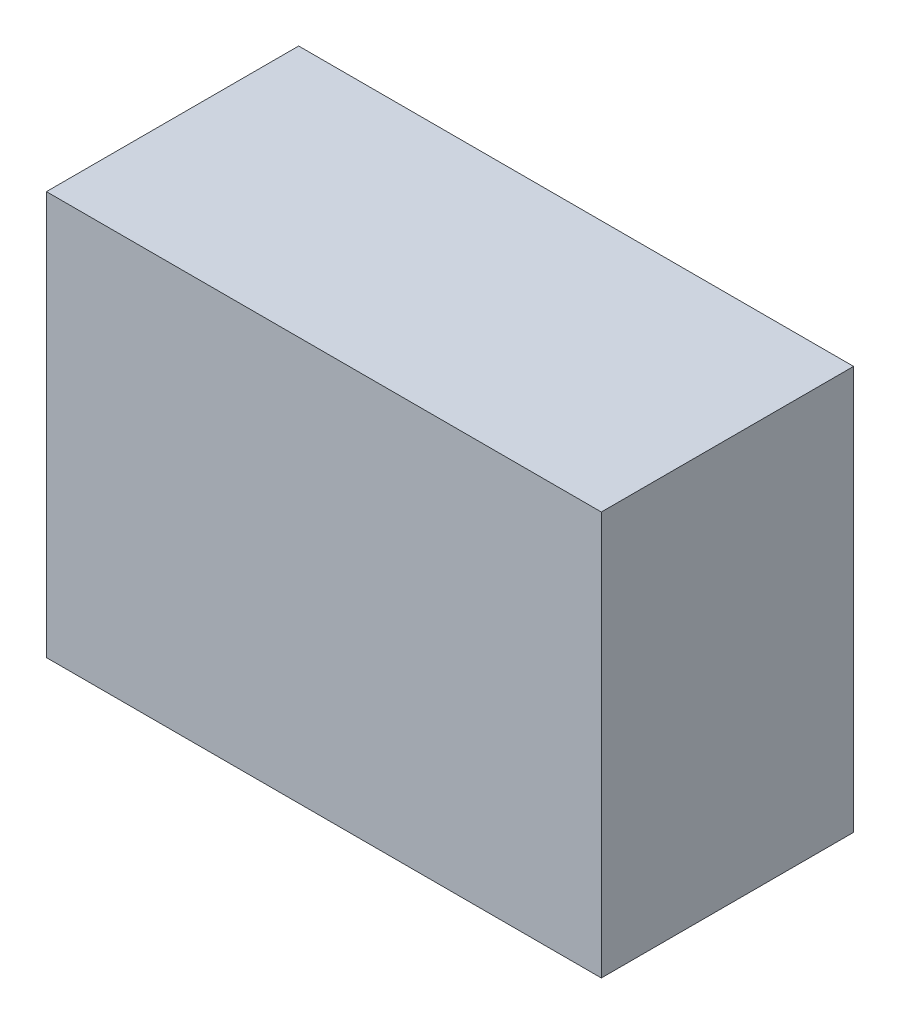
SolidWorks part; units mm, degrees
ref_plane "Front Plane" through (0, 0, 0) normal (0, 0, 1) x (1, 0, 0)
ref_plane "Top Plane" through (0, 0, 0) normal (0, 1, 0) x (1, 0, 0)
ref_plane "Right Plane" through (0, 0, 0) normal (1, 0, 0) x (0, 0, -1)
sketch "Sketch1" plane through (0, 0, 0) normal (0, 0, 1) x (1, 0, 0)
  line L1 (0, 0) -> (44, 0)
  line L2 (0, 0) -> (0, 32)
  line L3 (0, 32) -> (44, 32)
  line L4 (44, 0) -> (44, 32)
  dimension "D1" = 32
  dimension "D2" = 44
extrude "Boss-Extrude1" add sketch "Sketch1" along normal blind 20
